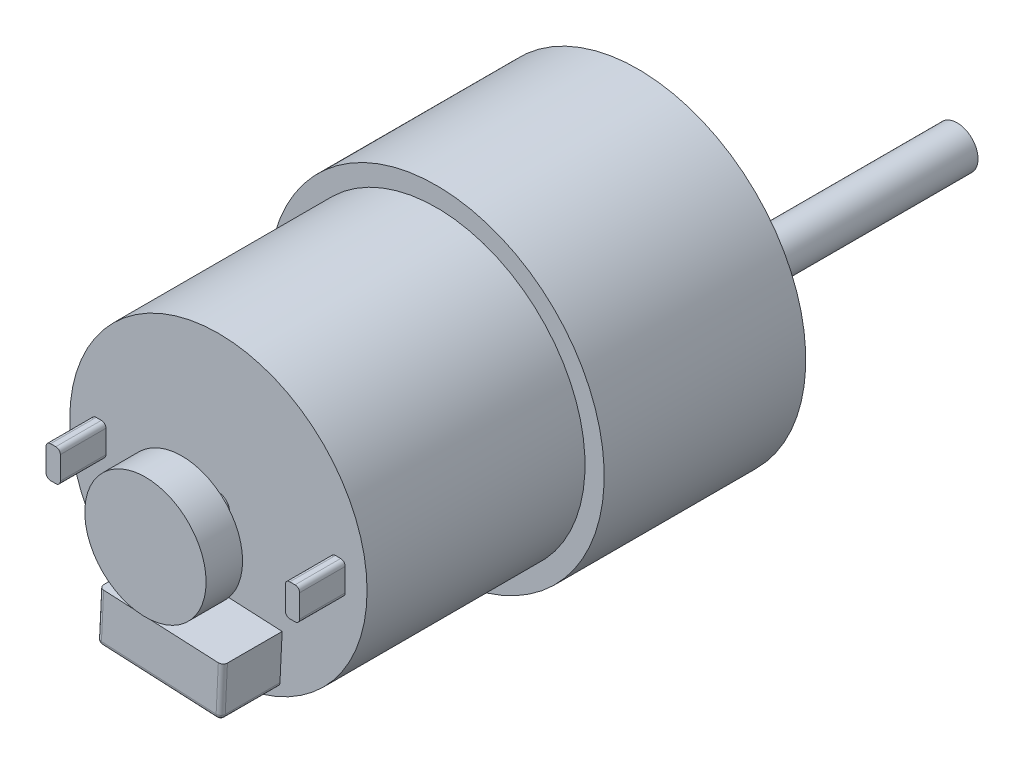
SolidWorks part; units mm, degrees
ref_plane "Front Plane" through (0, 0, 0) normal (0, 0, 1) x (1, 0, 0)
ref_plane "Top Plane" through (0, 0, 0) normal (0, 1, 0) x (1, 0, 0)
ref_plane "Right Plane" through (0, 0, 0) normal (1, 0, 0) x (0, 0, -1)
sketch "Sketch1" plane through (0, 0, 0) normal (0, 0, 1) x (1, 0, 0)
  line L1 (0, 18.4) -> (0, -6.5)
  circle A0 centre (0, 0) radius 16.3
  circle A1 centre (0, 0) radius 18.4
  circle A4 centre (0, -6.5) radius 5.9
  circle A5 centre (0, -6.5) radius 3
extrude "Boss-Extrude1" add sketch "Sketch1" along normal blind 46
sketch "Sketch2" plane through (0, 0, 0) normal (0, 0, -1) x (-1, 0, 0)
  circle A0 centre (0, 0) radius 18.4
  dimension "D1" = 36.8
extrude "Boss-Extrude2" add sketch "Sketch2" against normal blind 22.1
sketch "Sketch3" plane through (0, 0, 0) normal (0, 0, -1) x (-1, 0, 0)
  line L0 (0, 18.4) -> (0, -6.5) construction
  circle A0 centre (0, 0) radius 18.4 construction
  circle A1 centre (0, -6.5) radius 5.9
  circle A2 centre (0, -6.5) radius 2.2893
  dimension "D2" = 11.8
  dimension "D1" = 24.9
extrude "Boss-Extrude3" add sketch "Sketch3" along normal blind 5.5
sketch "Sketch4" plane through (0, 0, 0) normal (0, 0, -1) x (-1, 0, 0)
  circle A0 centre (0, -6.5) radius 2.2893
extrude "Boss-Extrude4" add sketch "Sketch4" along normal blind 35
sketch "Sketch5" plane through (0, 0, 0) normal (0, 0, -1) x (-1, 0, 0)
  circle A0 centre (0, 0) radius 15.4
  dimension "D1" = 30.8
extrude "Boss-Extrude5" add sketch "Sketch5" along normal blind 0.02
ref_plane "Plane1" through (0, 0, 46) normal (0, 0, 1) x (1, 0, 0)
sketch "Sketch7" plane through (0, 0, 46) normal (0, 0, 1) x (1, 0, 0)
  circle A0 centre (0, 0) radius 1.2193
  dimension "D1" = 2.4385
extrude "Boss-Extrude6" add sketch "Sketch7" along normal blind 4
ref_plane "Plane2" through (0, 0, 50) normal (0, 0, 1) x (1, 0, 0)
sketch "Sketch8" plane through (0, 0, 50) normal (0, 0, 1) x (1, 0, 0)
  circle A0 centre (0, 0) radius 6.65
  dimension "D1" = 13.3
extrude "Boss-Extrude7" add sketch "Sketch8" along normal blind 4
sketch "Sketch9" plane through (0, 0, 46) normal (0, 0, 1) x (1, 0, 0)
  line L0 (0, 18.4) -> (0, -18.4) construction
  line L1 (6.7237, -14.006) -> (-6.8483, -13.347)
  line L2 (6.7237, -14.006) -> (6.9905, -8.5125)
  line L3 (-6.8483, -13.347) -> (-6.5816, -7.8535)
  line L4 (6.9905, -8.5125) -> (-6.5816, -7.8535)
  line L5 (6.7237, -14.006) -> (-6.5816, -7.8535) construction
  line L6 (-6.8483, -13.347) -> (6.9905, -8.5125) construction
  circle A0 centre (0, 0) radius 18.4 construction
  point P6 (0.0711, -10.9297)
  dimension "D1" = 5.5
  dimension "D2" = 13.572
extrude "Boss-Extrude9" add sketch "Sketch9" along normal blind 6.5
fillet "Fillet3" radius 0.5 3 edges at (-6.8483, -13.347, 49.25) (-0.0623, -13.6765, 52.5) (-6.7149, -10.6003, 52.5)
fillet "Fillet4" radius 0.5 3 edges at (6.7308, -13.8597, 52.3536) (6.7237, -14.006, 49) (6.8692, -11.0095, 52.5)
sketch "Sketch10" plane through (0, 0, 46) normal (0, 0, 1) x (1, 0, 0)
  line L0 (-16.3, 0) -> (16.3, 0) construction
  line L1 (-16.3, 0) -> (-13.3, 0)
  line L2 (16.3, 0) -> (13.3, 0)
  line L3 (-13.9037, 1.1177) -> (-13.9037, -1.3957)
  line L4 (-13.4037, 1.6177) -> (-12.8297, 1.6177)
  line L5 (-13.4037, -1.8957) -> (-12.8297, -1.8957)
  line L6 (-12.3297, 1.1177) -> (-12.3297, -1.3957)
  line L7 (0, 0) -> (0, 10.8014) construction
  line L8 (13.4037, -1.8957) -> (12.8297, -1.8957)
  line L9 (13.9037, 1.1177) -> (13.9037, -1.3957)
  line L10 (13.4037, 1.6177) -> (12.8297, 1.6177)
  line L11 (12.3297, 1.1177) -> (12.3297, -1.3957)
  circle A0 centre (0, 0) radius 16.3 construction
  circle A1 centre (0, 0) radius 16.3 construction
  arc A2 (-13.4037, 1.6177) -> (-13.9037, 1.1177) centre (-13.4037, 1.1177) ccw
  arc A3 (-12.3297, 1.1177) -> (-12.8297, 1.6177) centre (-12.8297, 1.1177) ccw
  arc A4 (-13.4037, -1.8957) -> (-13.9037, -1.3957) centre (-13.4037, -1.3957) cw
  arc A5 (-12.8297, -1.8957) -> (-12.3297, -1.3957) centre (-12.8297, -1.3957) ccw
  arc A6 (12.8297, -1.8957) -> (12.3297, -1.3957) centre (12.8297, -1.3957) cw
  arc A7 (13.4037, -1.8957) -> (13.9037, -1.3957) centre (13.4037, -1.3957) ccw
  arc A8 (13.4037, 1.6177) -> (13.9037, 1.1177) centre (13.4037, 1.1177) cw
  arc A9 (12.3297, 1.1177) -> (12.8297, 1.6177) centre (12.8297, 1.1177) cw
  dimension "D3" = 0.5
  dimension "D4" = 0.5
  dimension "D5" = 0.5
  dimension "D6" = 0.5
  dimension "D1" = 3
  dimension "D2" = 3
extrude "Boss-Extrude10" add sketch "Sketch10" along normal blind 5
